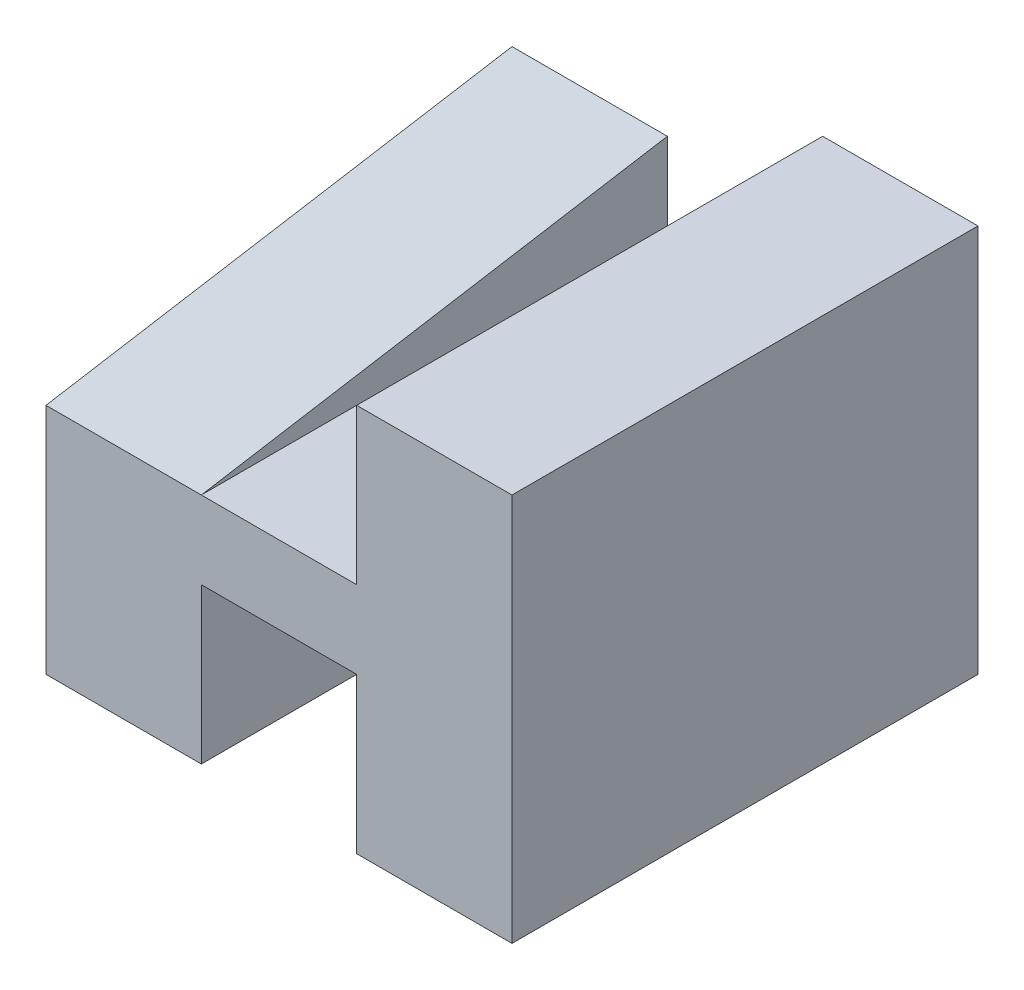
SolidWorks part; units mm, degrees
ref_plane "Front" through (0, 0, 0) normal (0, 0, 1) x (1, 0, 0)
ref_plane "Top" through (0, 0, 0) normal (0, 1, 0) x (1, 0, 0)
ref_plane "Right" through (0, 0, 0) normal (1, 0, 0) x (0, 0, -1)
sketch "Sketch1" plane through (0, 0, 0) normal (0, 1, 0) x (1, 0, 0)
  line L1 (-3, -3) -> (3, -3)
  line L2 (-3, -3) -> (-3, 3)
  line L3 (-3, 3) -> (3, 3)
  line L4 (3, -3) -> (3, 3)
  line L5 (-3, -3) -> (3, 3) construction
  line L6 (-3, 3) -> (3, -3) construction
  point P0 (0, 0)
  dimension "D1" = 6
  dimension "D2" = 6
extrude "Boss-Extrude1" add sketch "Sketch1" along normal blind 5
sketch "Sketch2" plane through (0, 0, 0) normal (1, 0, 0) x (0, 0, -1)
  line L0 (3, 0) -> (-3, 2)
  line L1 (-3, 5) -> (-3, 0) construction
  line L2 (-3, 2) -> (-3, 0)
  line L3 (-3, 0) -> (3, 0)
  line L4 (3, 5) -> (3, 0) construction
  line L5 (3, 3) -> (-3, 3)
  line L6 (3, 3) -> (3, 5)
  line L7 (3, 5) -> (-3, 5)
  line L8 (-3, 3) -> (-3, 5)
  dimension "D1" = 2
  dimension "D2" = 2
extrude "Cut-Extrude1" cut sketch "Sketch2" against normal mid plane 2
sketch "Sketch3" plane through (-3, 0, 0) normal (-1, 0, 0) x (0, 0, 1)
  line L0 (3, 3) -> (-3, 4)
  line L6 (-3, 0) -> (3, 0)
  line L7 (3, 0) -> (3, 5)
  line L8 (3, 5) -> (-3, 5)
  line L9 (-3, 5) -> (-3, 0)
  line L10 (-3, 0) -> (3, 0)
  line L11 (3, 0) -> (3, 5)
  line L12 (3, 5) -> (-3, 5)
  line L13 (-3, 5) -> (-3, 0)
  line M6 (3, 0) -> (3, 5)
  line M7 (3, 5) -> (-3, 5)
  line M8 (-3, 5) -> (-3, 0)
  dimension "D2" = 2
  dimension "D3" = 1
  dimension "D1" = 0
extrude "Cut-Extrude2" cut sketch "Sketch3" against normal blind 2 contours L0 M6 M7 M8
